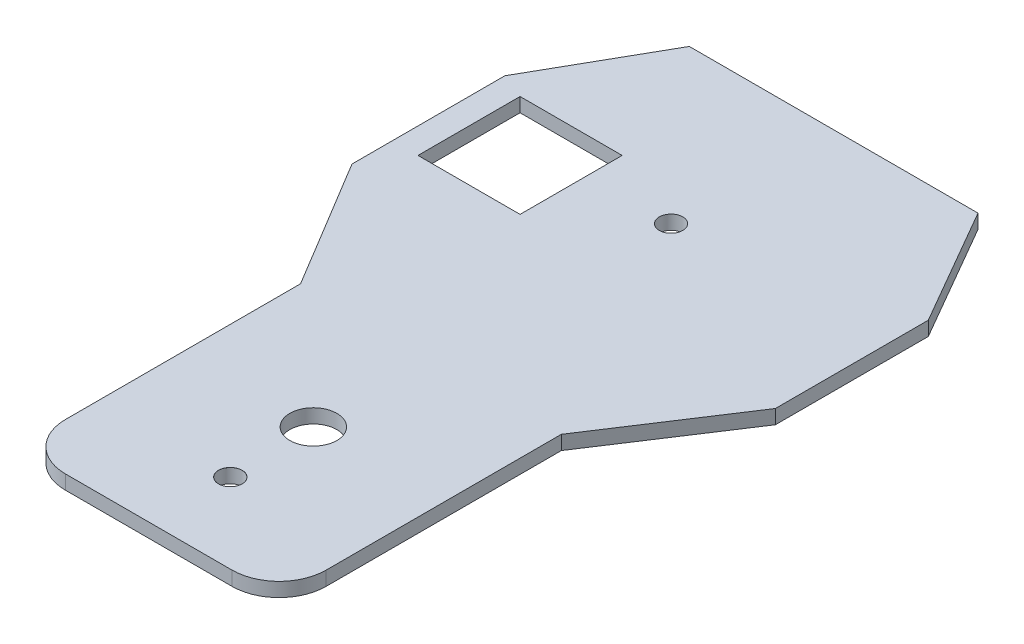
SolidWorks part; units mm, degrees
other "Markup1"
sketch "Sketch34" plane through (-37.6247, -94.9368, 127.0632) normal (-0.3668, 0.8085, 0.4601) x (0.7471, -0.0387, 0.6636)
material "Oak"
ref_plane "Front Plane" through (0, 0, 0) normal (0, 0, 1) x (1, 0, 0)
ref_plane "Top Plane" through (0, 0, 0) normal (0, 1, 0) x (1, 0, 0)
ref_plane "Right Plane" through (0, 0, 0) normal (1, 0, 0) x (0, 0, -1)
sketch "Sketch6" plane through (0, 0, 0) normal (0, 0, 1) x (1, 0, 0)
  line L0 (-61.3636, 0) -> (61.3636, 0)
  line L1 (-61.3636, 0) -> (-89.7689, -50)
  line L2 (61.3636, 0) -> (90.2311, -50)
  line L3 (-89.7689, -50) -> (-89.7689, -115)
  line L4 (90.2311, -50) -> (90.2311, -115)
  line L5 (-89.7689, -82.5) -> (90.2311, -82.5) construction
  line L6 (0, 0) -> (0, -292.2204) construction
  line L8 (-89.7689, -115) -> (-56.6221, -170)
  line L9 (54.2374, -170) -> (90.2311, -115)
  line L10 (-56.6221, -170) -> (-56.6221, -290)
  line L11 (54.2374, -170) -> (54.2374, -290)
  line L12 (-56.6221, -290) -> (54.2374, -290)
  point P4 (0, 0)
  point P15 (0, -169.8746)
  dimension "D1" = 180
  dimension "D2" = 50
  dimension "D3" = 50
  dimension "D4" = 122.7273
  dimension "D5" = 65
  dimension "D6" = 65
  dimension "D7" = 55
  dimension "D8" = 55
  dimension "D9" = 120
  dimension "D10" = 120
extrude "Boss-Extrude1" add sketch "Sketch6" along normal blind 6
fillet "Fillet1" radius 20 1 edges at (54.2374, -290, 3)
fillet "Fillet2" radius 20 1 edges at (-56.6221, -290, 3)
sketch "Sketch30" plane through (0, 0, 0) normal (0, 0, 1) x (1, 0, 0)
  line L0 (-1.1924, -290) -> (-1.1924, -220) construction
  line L1 (-36.6221, -290) -> (34.2374, -290) construction
  circle A0 centre (-1.1924, -220) radius 10
extrude "Cut-Extrude44" cut sketch "Sketch30" along normal through all both and the other way through all
sketch "Sketch31" plane through (0, 0, 6) normal (0, 0, 1) x (1, 0, 0)
  circle A0 centre (0, -69.1336) radius 5
  point P2 (0, -69.1336)
extrude "Cut-Extrude45" cut sketch "Sketch31" against normal blind 10
split "Split1" trim tools "Front Plane" bodies to split 151 resulting bodies 137
move or copy body "Body-Move/Copy3" bodies to move or copy 137 copy no rotation origin (0, -121.9368, -1) rotation axis (1, 0, 0) rotation angle 90
move or copy body "Body-Move/Copy4" bodies to move or copy 141 copy no rotation origin (0, -111.9368, -21) rotation axis (1, 0, 0) rotation angle 180
move or copy body "Body-Move/Copy5" bodies to move or copy 142 copy no translate (52.1441, 0, 0)
hole_wizard "Ø10.0mm Dowel Hole1" positions "Sketch32" profile "Sketch33" hole size "Ø10.0" standard "GB"
sketch "Sketch32" plane through (0, -94.9368, 0) normal (0, 1, 0) x (1, 0, 0)
  point P0 (51.7614, -93.1781)
sketch "Sketch33" plane through (51.7614, -94.9368, 93.1781) normal (1, 0, 0) x (0, 0, 1)
  line L0 (0, 0) -> (0, 53.0043)
  line L1 (0, 53.0043) -> (5, 50)
  line L2 (5, 50) -> (5, 0.025)
  line L3 (5, 0.025) -> (5.025, 0)
  line L5 (5.025, 0) -> (0, 0)
  line L6 (-5, 0.025) -> (-5.025, 0) construction
  line L10 (0, 53.0043) -> (-5, 50) construction
  line L11 (0, -6.35) -> (0, 107.95) construction
  dimension "Hole Dia." = 10
  dimension "Hole Depth" = 50
  dimension "Near C'Sink Dia." = 10.05
  dimension "Near C'Sink Angle" = 90
  dimension "Drill Angle" = 118
sketch "Sketch35" plane through (0, 0, 0) normal (0, 1, 0) x (1, 0, 0)
  line L0 (-26.7629, 108.5265) -> (16.6371, 108.5265)
  line L1 (-26.7629, 108.5265) -> (-26.7629, 65.1265)
  line L2 (-26.7629, 65.1265) -> (16.6371, 65.1265)
  line L3 (16.6371, 65.1265) -> (16.6371, 108.5265)
extrude "Cut-Extrude46" cut sketch "Sketch35" against normal blind 200
